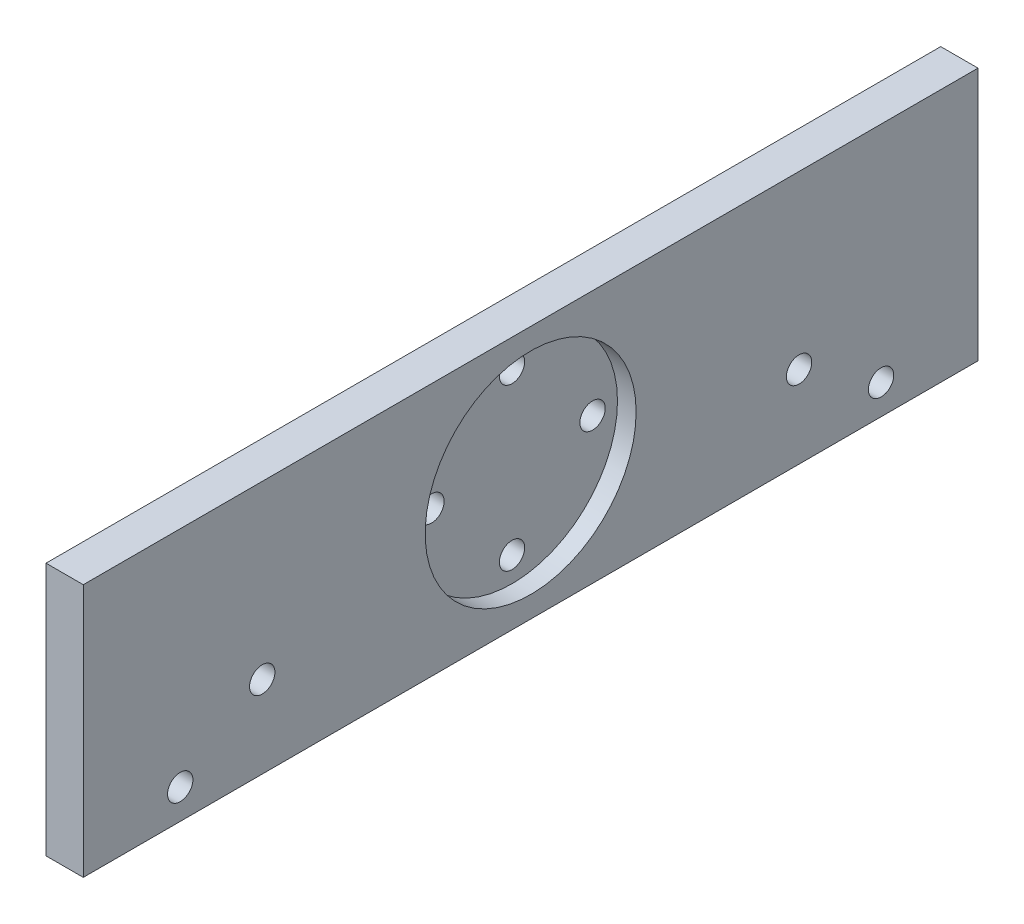
SolidWorks part; units mm, degrees
material "1060 Alloy"
ref_plane "Front" through (0, 0, 0) normal (0, 0, 1) x (1, 0, 0)
ref_plane "Top" through (0, 0, 0) normal (0, 1, 0) x (1, 0, 0)
ref_plane "Right" through (0, 0, 0) normal (1, 0, 0) x (0, 0, -1)
sketch "Sketch1" plane through (0, 0, 0) normal (1, 0, 0) x (0, 0, -1)
  line L1 (0, 0) -> (-120, 0)
  line L2 (0, 0) -> (0, 34)
  line L3 (0, 34) -> (-120, 34)
  line L4 (-120, 0) -> (-120, 34)
  dimension "D1" = 34
  dimension "D2" = 120
extrude "Boss-Extrude1" add sketch "Sketch1" along normal blind 5
sketch "Sketch2" plane through (5, 0, 0) normal (1, 0, 0) x (0, 0, -1)
  line L0 (-60, 34) -> (-60, 0)
  line L1 (0, 34) -> (-120, 34) construction
  line L2 (0, 0) -> (-120, 0) construction
  circle A0 centre (-60, 17) radius 14.15
  dimension "D1" = 28.3
extrude "Cut-Extrude1" cut sketch "Sketch2" against normal blind 2.5 contours L0 A0 | L0 A0
hole_wizard "M3 Clearance Hole1" positions "Sketch4" profile "Sketch3" hole size "M3" standard "ISO"
sketch "Sketch4" plane through (2.5, 0, 0) normal (1, 0, 0) x (0, 0, -1)
  circle A0 centre (-60, 17) radius 14.15 construction
  circle A1 centre (-60, 17) radius 14.15 construction
  point P0 (-60, 27.8)
  point P10 (-49.2, 17)
  point P11 (-60, 6.2)
  point P12 (-70.8, 17)
  dimension "D1" = 10.8
  dimension "D3" = 0
  dimension "D4" = 10.8
  dimension "D6" = 0
  dimension "D2" = 4
sketch "Sketch3" plane through (2.5, 27.8, 60) normal (0, 1, 0) x (0, 0, -1)
  line L0 (0, 0) -> (0, 16.0215)
  line L1 (0, 16.0215) -> (1.7, 15)
  line L2 (1.7, 15) -> (1.7, 0)
  line L5 (1.7, 0) -> (0, 0)
  line L10 (0, 16.0215) -> (-1.7, 15) construction
  line L11 (0, -6.35) -> (0, 107.95) construction
  dimension "Hole Dia." = 3.4
  dimension "Hole Depth" = 15
  dimension "Drill Angle" = 118
hole_wizard "M3 Clearance Hole3" positions "Sketch8" profile "Sketch7" hole size "M3" standard "ISO"
sketch "Sketch8" plane through (0, 0, 0) normal (-1, 0, 0) x (0, 0, 1)
  line L0 (0, 0) -> (0, 34) construction
  line L1 (0, 0) -> (120, 0) construction
  line L2 (120, 0) -> (120, 34) construction
  point P0 (24, 11)
  point P3 (13, 4)
  point P6 (96, 11)
  point P9 (107, 4)
  dimension "D1" = 13
  dimension "D2" = 4
  dimension "D3" = 11
  dimension "D4" = 7
  dimension "D5" = 7
  dimension "D6" = 11
  dimension "D7" = 4
  dimension "D8" = 13
sketch "Sketch7" plane through (0, 11, 24) normal (0, 1, 0) x (0, 0, 1)
  line L0 (0, 0) -> (0, 16.0215)
  line L1 (0, 16.0215) -> (1.7, 15)
  line L2 (1.7, 15) -> (1.7, 0)
  line L5 (1.7, 0) -> (0, 0)
  line L10 (0, 16.0215) -> (-1.7, 15) construction
  line L11 (0, -6.35) -> (0, 107.95) construction
  dimension "Hole Dia." = 3.4
  dimension "Hole Depth" = 15
  dimension "Drill Angle" = 118
